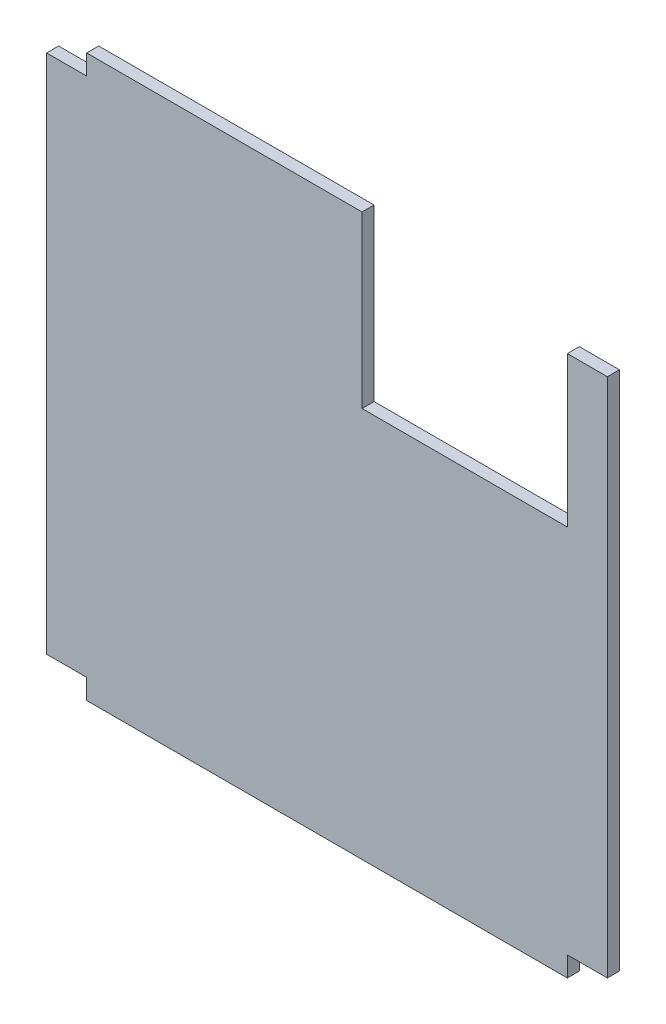
SolidWorks part; units mm, degrees
material "ﾊﾞﾙｻ"
ref_plane "正面" through (0, 0, 0) normal (0, 0, 1) x (1, 0, 0)
ref_plane "平面" through (0, 0, 0) normal (0, 1, 0) x (1, 0, 0)
ref_plane "右側面" through (0, 0, 0) normal (1, 0, 0) x (0, 0, -1)
sketch "ｽｹｯﾁ1" plane through (0, 0, 0) normal (0, 0, 1) x (1, 0, 0)
  line L0 (0, 0) -> (480, 0)
  line L1 (0, 0) -> (0, -20)
  line L2 (0, -20) -> (-40, -20)
  line L3 (480, 0) -> (480, -20)
  line L4 (480, -20) -> (520, -20)
  line L5 (520, -20) -> (520, -540)
  line L6 (520, -540) -> (480, -540)
  line L7 (480, -540) -> (480, -560)
  line L8 (480, -560) -> (0, -560)
  line L9 (0, -560) -> (0, -540)
  line L10 (0, -540) -> (-40, -540)
  line L11 (-40, -540) -> (-40, -20)
  dimension "D1" = 480
  dimension "D2" = 20
  dimension "D3" = 40
  dimension "D4" = 20
  dimension "D5" = 40
  dimension "D6" = 520
  dimension "D7" = 40
  dimension "D8" = 20
  dimension "D9" = 480
  dimension "D10" = 20
  dimension "D11" = 40
  dimension "D12" = 90
  dimension "D13" = 520
extrude "ﾎﾞｽ - 押し出し1" add sketch "ｽｹｯﾁ1" along normal blind 12 contours L11 L2 L1 L0 L3 L4 L5 L6 L7 L8 L9 L10
sketch "ｽｹｯﾁ3" plane through (0, 0, 12) normal (0, 0, 1) x (1, 0, 0)
  line L0 (0, 0) -> (480, 0) construction
  line L1 (480, 0) -> (275, 0)
  line L2 (480, 0) -> (480, -170)
  line L3 (480, -170) -> (275, -170)
  line L4 (275, 0) -> (275, -170)
  line L5 (480, 0) -> (480, -20) construction
  dimension "D1" = 170
  dimension "D2" = 205
extrude "ｶｯﾄ - 押し出し2" cut sketch "ｽｹｯﾁ3" against normal blind 12
sketch "ｽｹｯﾁ4" plane through (480, 0, 0) normal (-1, 0, 0) x (0, 0, 1)
  line L1 (0, -20) -> (12, -20)
  line L2 (0, -20) -> (0, -170)
  line L3 (0, -170) -> (12, -170)
  line L4 (12, -20) -> (12, -170)
extrude "ﾎﾞｽ - 押し出し2" add sketch "ｽｹｯﾁ4" along normal blind 2
sketch "ｽｹｯﾁ5" plane through (0, -20, 0) normal (0, 1, 0) x (1, 0, 0)
  line L0 (478, 0) -> (520, 0) construction
  line L1 (478, -12) -> (480, -12)
  line L2 (478, -12) -> (478, 0)
  line L3 (478, 0) -> (480, 0)
  line L4 (480, -12) -> (480, 0)
  dimension "D1" = 2
extrude "ｶｯﾄ - 押し出し3" cut sketch "ｽｹｯﾁ5" against normal blind 150
ref_plane "平面1" through (480, -20, 0) normal (0, 0, -1) x (-1, 0, 0)
